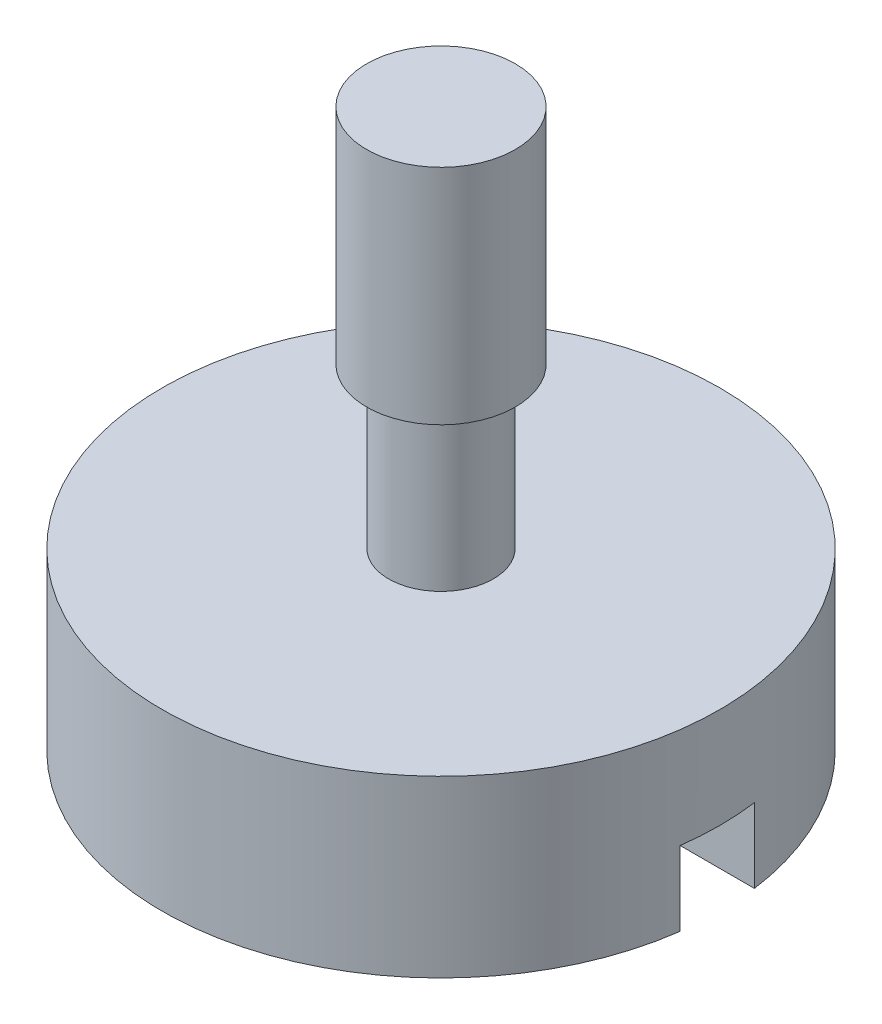
SolidWorks part; units mm, degrees
material "Acciaio in lega fuso"
ref_plane "Piano frontale" through (0, 0, 0) normal (0, 0, 1) x (1, 0, 0)
ref_plane "Piano superiore" through (0, 0, 0) normal (0, 1, 0) x (1, 0, 0)
ref_plane "Piano destro" through (0, 0, 0) normal (1, 0, 0) x (0, 0, -1)
sketch "Schizzo1" plane through (0, 0, 0) normal (0, 0, 1) x (1, 0, 0)
  line L0 (0, 15) -> (2, 15)
  line L1 (2, 15) -> (2, 9)
  line L2 (1.4095, 4.7) -> (7.5, 4.7)
  line L3 (7.5, 4.7) -> (7.5, 0)
  line L4 (7.5, 0) -> (0, 0)
  line L5 (0, 0) -> (0, 15)
  line L6 (0, -3.5783) -> (0, 18.4871) construction
  line L7 (2, 9) -> (1.4095, 9)
  line L8 (1.4095, 9) -> (1.4095, 4.7)
  dimension "D1" = 15
  dimension "D2" = 4.7
  dimension "D3" = 15
  dimension "D4" = 6
  dimension "D5" = 4
revolve "Rivoluzione1" add sketch "Schizzo1" angle 360 about L6
sketch "Schizzo2" plane through (0, 0, 0) normal (0, -1, 0) x (1, 0, 0)
  line L1 (-10.0578, 1) -> (10.0578, 1)
  line L2 (-10.0578, 1) -> (-10.0578, -1)
  line L3 (-10.0578, -1) -> (10.0578, -1)
  line L4 (10.0578, 1) -> (10.0578, -1)
  line L5 (-10.0578, 1) -> (10.0578, -1) construction
  line L6 (-10.0578, -1) -> (10.0578, 1) construction
  point P0 (0, 0)
  dimension "D1" = 2
extrude "Taglio-Estrusione1" cut sketch "Schizzo2" against normal blind 2
